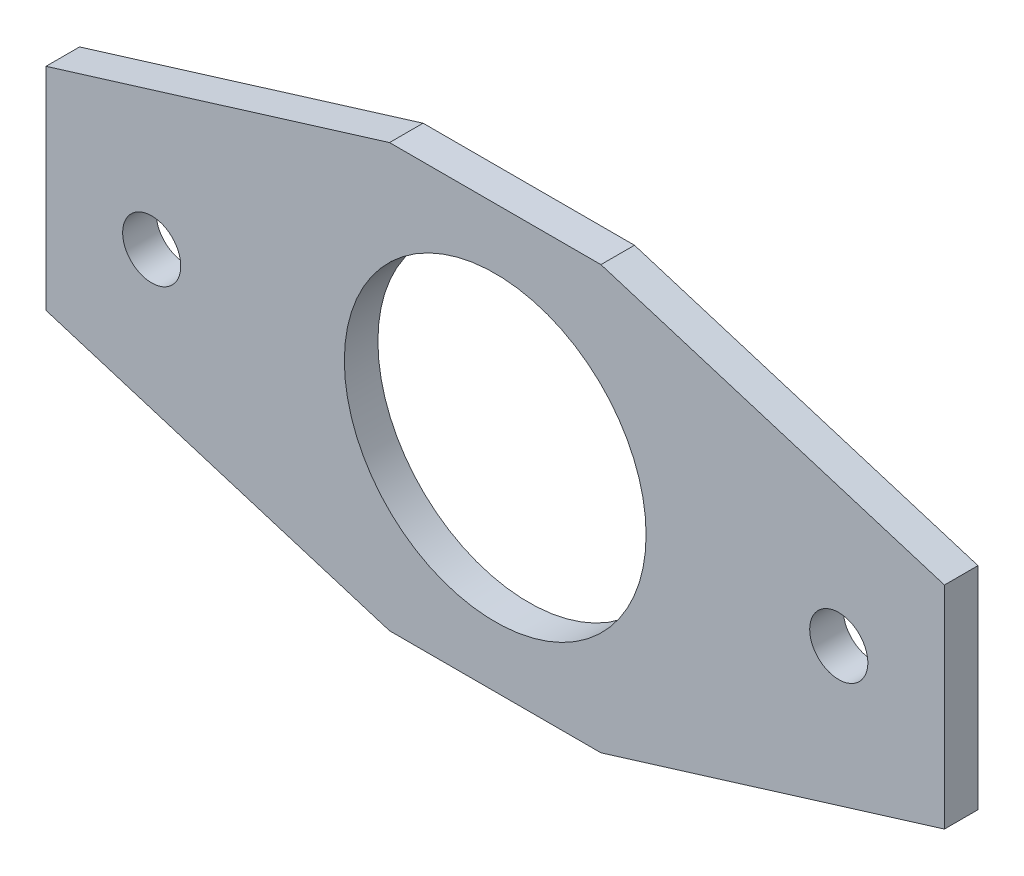
SolidWorks part; units mm, degrees
ref_plane "Front Plane" through (0, 0, 0) normal (0, 0, 1) x (1, 0, 0)
ref_plane "Top Plane" through (0, 0, 0) normal (0, 1, 0) x (1, 0, 0)
ref_plane "Right Plane" through (0, 0, 0) normal (1, 0, 0) x (0, 0, -1)
sketch "Sketch1" plane through (0, 0, 0) normal (0, 0, 1) x (1, 0, 0)
  line L1 (0, 0) -> (85, 0)
  line L2 (0, 0) -> (0, 40)
  line L3 (0, 40) -> (85, 40)
  line L4 (85, 0) -> (85, 40)
  dimension "D1" = 40
  dimension "D2" = 85
extrude "Boss-Extrude1" add sketch "Sketch1" along normal blind 3.175
sketch "Sketch2" plane through (0, 0, 3.175) normal (0, 0, 1) x (1, 0, 0)
  line L0 (85, 40) -> (0, 40) construction
  line L2 (0, 40) -> (0, 0) construction
  circle A0 centre (42.5, 20) radius 14.275
  point P5 (42.5, 40)
  point P8 (0, 20)
  dimension "D1" = 28.55
extrude "Cut-Extrude1" cut sketch "Sketch2" against normal through all
sketch "Sketch4" plane through (0, 0, 0) normal (0, 0, -1) x (-1, 0, 0)
  line L0 (-32.5, 40) -> (0, 30)
  line L1 (-85, 40) -> (0, 40) construction
  line L2 (0, 40) -> (0, 0) construction
  line L3 (0, 30) -> (0, 10)
  line L4 (0, 10) -> (-32.5, 0)
  line L5 (0, 0) -> (-85, 0) construction
  line L6 (-32.5, 0) -> (-52.5, 0)
  line L7 (-52.5, 0) -> (-85, 10)
  line L8 (-85, 0) -> (-85, 40) construction
  line L9 (-85, 10) -> (-85, 30)
  line L10 (-85, 30) -> (-52.5, 40)
  line L13 (-52.5, 40) -> (-32.5, 40)
  point P11 (-85, 20)
  point P17 (-85, 20)
  point P18 (-42.5, 40)
  point P19 (-42.5, 40)
  point P20 (-42.5, 0)
  point P21 (-42.5, 0)
  point P22 (0, 20)
  point P23 (0, 20)
  dimension "D1" = 20
  dimension "D2" = 20
  dimension "D3" = 20
  dimension "D4" = 20
extrude "Cut-Extrude4" cut sketch "Sketch4" against normal through all flip side to cut
sketch "Sketch6" plane through (0, 0, 0) normal (0, 0, -1) x (-1, 0, 0)
  line L0 (0, 30) -> (0, 10) construction
  line L1 (-85, 20) -> (0, 20) construction
  line L2 (-85, 10) -> (-85, 30) construction
  circle A0 centre (-75, 20) radius 2.75
  circle A1 centre (-10, 20) radius 2.75
  dimension "D3" = 5.5
  dimension "D4" = 5.5
  dimension "D1" = 10
  dimension "D2" = 10
extrude "Cut-Extrude6" cut sketch "Sketch6" against normal through all
